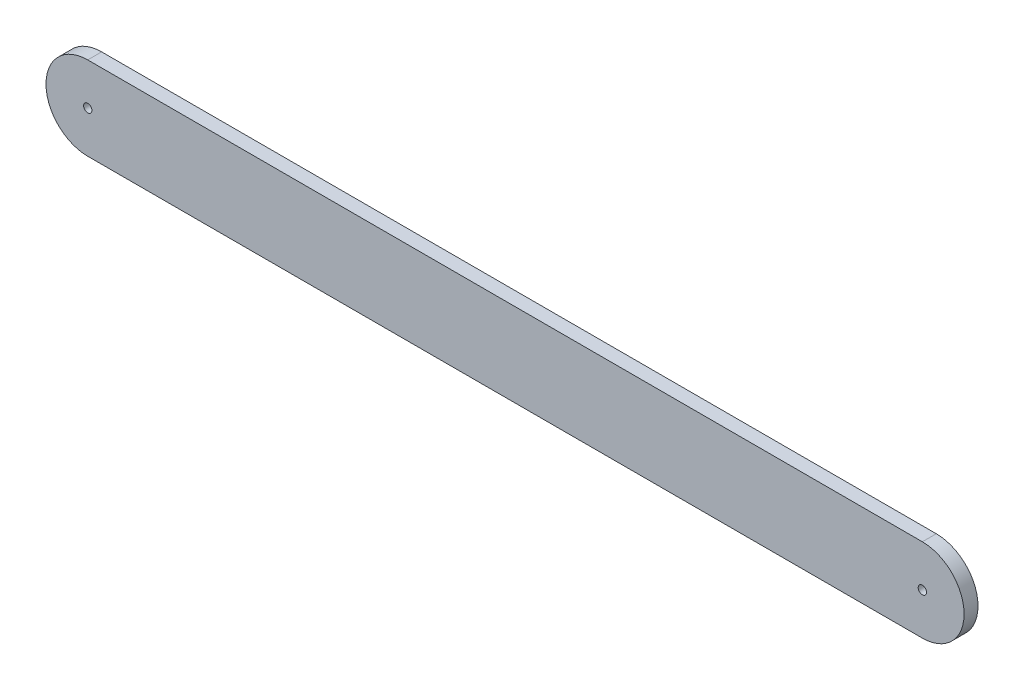
SolidWorks part; units mm, degrees
ref_plane "Front Plane" through (0, 0, 0) normal (0, 0, 1) x (1, 0, 0)
ref_plane "Top Plane" through (0, 0, 0) normal (0, 1, 0) x (1, 0, 0)
ref_plane "Right Plane" through (0, 0, 0) normal (1, 0, 0) x (0, 0, -1)
sketch "Sketch1" plane through (0, 0, 0) normal (0, 0, 1) x (1, 0, 0)
  line L0 (-133.9939, 0) -> (166.0061, 0) construction
  line L1 (-133.9939, 0) -> (166.0061, 0) construction
  line L2 (-133.9939, 15) -> (166.0061, 15)
  line L3 (-133.9939, -15) -> (166.0061, -15)
  arc A0 (-133.9939, 15) -> (-133.9939, -15) centre (-133.9939, 0) ccw
  arc A1 (166.0061, -15) -> (166.0061, 15) centre (166.0061, 0) ccw
  circle A2 centre (-133.9939, 0) radius 1.5
  circle A3 centre (166.0061, 0) radius 1.5
  point P3 (16.0061, 0)
  dimension "D3" = 3
  dimension "D4" = 3
  dimension "D1" = 300
  dimension "D2" = 30
extrude "Boss-Extrude1" add sketch "Sketch1" along normal blind 5
